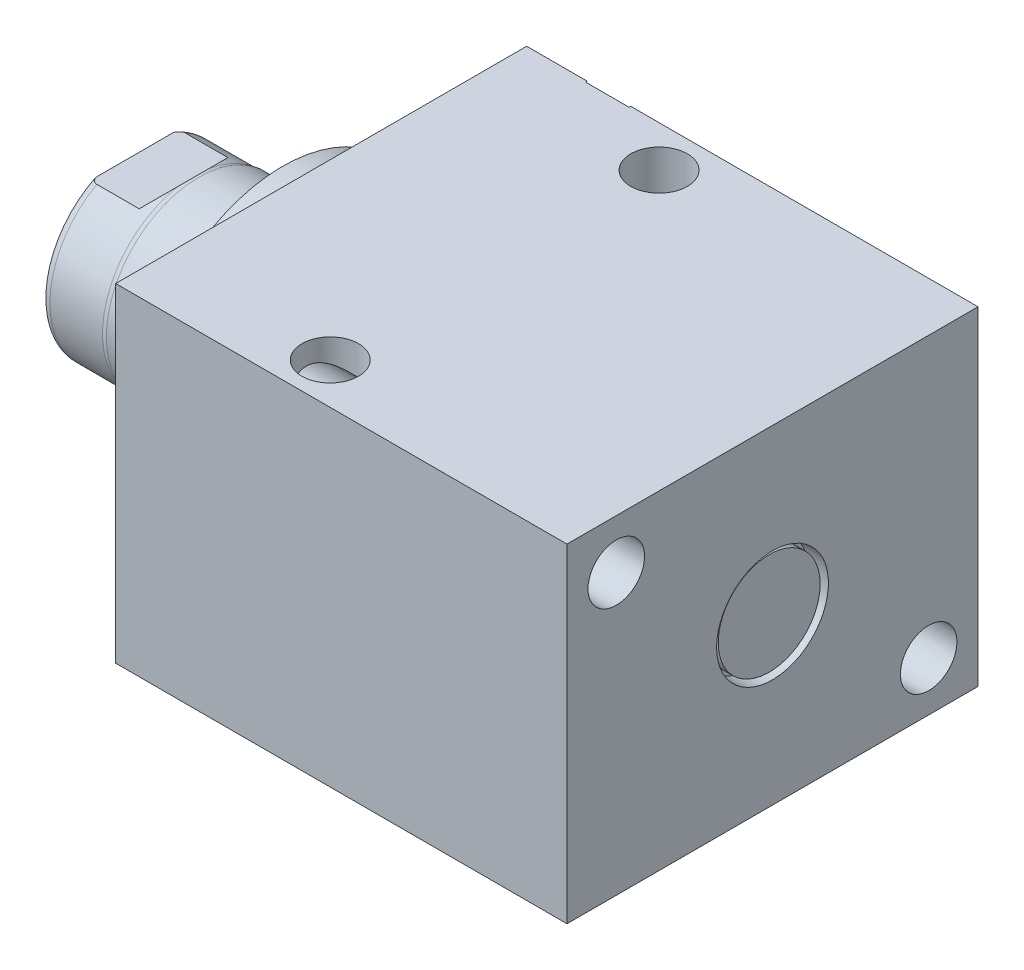
SolidWorks part; units mm, degrees
material "Alloy Steel"
ref_plane "Front Plane" through (0, 0, 0) normal (0, 0, 1) x (1, 0, 0)
ref_plane "Top Plane" through (0, 0, 0) normal (0, 1, 0) x (1, 0, 0)
ref_plane "Right Plane" through (0, 0, 0) normal (1, 0, 0) x (0, 0, -1)
ref_plane "Plane1" through (0, 0, 0) normal (1, 0, 0) x (0, 0, -1)
sketch "Sketch1" plane through (0, 0, 0) normal (1, 0, 0) x (0, 0, -1)
  line L0 (-31.75, 25.4) -> (31.75, 25.4)
  line L1 (31.75, 25.4) -> (31.75, -25.4)
  line L2 (31.75, -25.4) -> (-31.75, -25.4)
  line L3 (-31.75, -25.4) -> (-31.75, 25.4)
  line L4 (0, -24.4475) -> (0, 24.4475) construction
  dimension "D1" = 50.8
  dimension "D2" = 25.4
  dimension "D3" = 63.5
  dimension "D4" = 31.75
extrude "Extrude1" add sketch "Sketch1" along normal blind 69.723
ref_plane "Plane12" through (0, 17.4498, 0) normal (0, 1, 0) x (-1, 0, 0)
sketch "S2D0002" plane through (0, 17.4498, 0) normal (0, 1, 0) x (-1, 0, 0)
  line L0 (-17.7165, -31.496) -> (-21.336, -31.496)
  line L1 (-17.7165, -31.4706) -> (-17.7165, -31.496)
  line L2 (-17.7165, -31.4706) -> (-17.1196, -30.8737)
  line L3 (-17.1196, -30.8737) -> (-17.1196, -18.034)
  line L4 (-17.1196, -18.034) -> (-12.7, -18.034)
  line L5 (-12.7, -18.034) -> (-12.7, -31.75)
  line L6 (-12.7, -19.1384) -> (-12.7, 0.6985) construction
  line L7 (0, -31.75) -> (0, 31.75) construction
  line L8 (-21.336, -31.75) -> (-21.336, -31.496)
  line L9 (-69.723, -31.75) -> (0, -31.75) construction
  line L10 (-21.336, -31.75) -> (-12.7, -31.75)
  dimension "D1" = 13.716
  dimension "D2" = 12.7
  dimension "D3" = 8.8392
  dimension "D4" = 45
  dimension "D5" = 0.6223
  dimension "D6" = 10.033
  dimension "D7" = 0.0254
  dimension "D8" = 0.254
  dimension "D9" = 17.272
revolve "Cut-Revolve1" cut sketch "S2D0002" angle 360 about L6
pattern_linear "LPattern1" count 2 spacing 41.148 along (1, 0, 0) count 2 spacing 17.4498 along (0, -1, 0) skipping (0, 1), (1, 0) of "Cut-Revolve1"
sketch "Sketch5" plane through (0, 0, 0) normal (-1, 0, 0) x (0, 0, 1)
  circle A0 centre (0, 0) radius 22.225
  dimension "D1" = 44.45
extrude "Extrude2" add sketch "Sketch5" along normal blind 5.969
ref_plane "Plane5" through (0, 0, 0) normal (0, -1, 0) x (0, 0, 1)
sketch "Sketch6" plane through (0, 0, 0) normal (0, -1, 0) x (0, 0, 1)
  line L0 (0, 5.969) -> (-14.2748, 5.969)
  line L1 (-14.2748, 5.969) -> (-14.2748, 28.829)
  line L2 (-14.2748, 28.829) -> (0, 28.829)
  line L3 (0, 28.829) -> (0, 5.969)
  line L4 (0, -5.7546) -> (0, 21.1709) construction
  line L5 (22.225, 5.969) -> (-22.225, 5.969) construction
  line L6 (31.75, -69.723) -> (-31.75, -69.723) construction
  dimension "D1" = 98.552
  dimension "D2" = 28.5496
revolve "Revolve1" add sketch "Sketch6" angle 360 about L4
ref_plane "Plane6" through (-18.5113, 3.2639, 0) normal (0, 0, 1) x (0, 1, 0)
sketch "S2D0001" plane through (-18.5113, 3.2639, 0) normal (0, 0, 1) x (0, 1, 0)
  line L0 (1.8669, 8.206) -> (1.8669, -6.5225)
  line L1 (-3.2639, -6.5225) -> (1.8669, -6.5225)
  line L2 (3.0861, 10.3177) -> (-3.2639, 10.3177)
  line L3 (-3.2639, 10.3177) -> (-3.2639, -6.5225)
  line L4 (1.8669, 8.206) -> (3.0861, 10.3177)
  line L5 (-3.2639, -18.5113) -> (-3.2639, 2.765) construction
  line L6 (11.0109, 10.3177) -> (-17.5387, 10.3177) construction
  dimension "D1" = 30
  dimension "D2" = 12.7
  dimension "D3" = 10.2616
  dimension "D4" = 16.8402
  dimension "D5" = 90
revolve "Cut-Revolve4" cut sketch "S2D0001" angle 360 about L5
ref_plane "Plane7" through (0, 0, 0) normal (0, 1, 0) x (0, 0, -1)
sketch "Sketch8" plane through (0, 0, 0) normal (0, 1, 0) x (0, 0, -1)
  line L0 (-14.2748, 18.923) -> (-14.097, 19.685)
  line L1 (-14.097, 19.685) -> (-14.097, 27.813)
  line L2 (0, 12.6594) -> (0, 20.8178) construction
  line L3 (-14.2748, 18.923) -> (-14.2748, 28.829)
  line L4 (-13.7089, 28.829) -> (-14.2748, 28.829)
  line L5 (14.2748, 28.829) -> (-14.2748, 28.829) construction
  line L6 (-14.2748, 28.829) -> (-14.2748, 5.969) construction
  arc A0 (-13.7089, 28.829) -> (-14.097, 27.813) centre (-12.573, 27.813) ccw
  dimension "D2" = 1.524
  dimension "D1" = 28.194
  dimension "D3" = 1.016
  dimension "D4" = 0.762
  dimension "D5" = 9.144
revolve "Cut-Revolve5" cut sketch "Sketch8" angle 360 about L2
ref_plane "Plane11" through (0, 0, 0) normal (0, 0, -1) x (0, -1, 0)
sketch "Sketch12" plane through (0, 0, 0) normal (0, 0, -1) x (0, -1, 0)
  line L0 (12.319, 28.829) -> (12.319, 21.2598)
  line L1 (12.319, 21.2598) -> (14.2748, 19.304)
  line L2 (-12.319, 28.829) -> (-12.319, 21.2598)
  line L3 (-12.319, 21.2598) -> (-14.2748, 19.304)
  line L4 (12.319, 28.829) -> (14.2748, 28.829)
  line L5 (0, 13.7262) -> (0, 20.767) construction
  line L6 (-14.2748, 19.304) -> (-14.2748, 28.829)
  line L7 (14.2748, 5.969) -> (14.2748, 18.923) construction
  line L9 (14.2748, 19.304) -> (14.2748, 28.829)
  line L10 (-12.319, 28.829) -> (-14.2748, 28.829)
  line L12 (13.7089, 28.829) -> (-13.7089, 28.829) construction
  dimension "D1" = 24.638
  dimension "D2" = 7.5692
  dimension "D3" = 45
extrude "Cut-Extrude4" cut sketch "Sketch12" against normal mid plane 60.96
hole_wizard "Hole1" positions "Sketch15" profile "Sketch14" legacy end condition up to next
sketch "Sketch15" plane through (0, 0, 0) normal (-1, 0, 0) x (0, 0, 1)
  line L0 (0, 0) -> (-29.9914, 0) construction
  line L1 (0, 0) -> (0, 25.7648) construction
  point P0 (-24.13, -17.78)
  point P11 (24.13, 17.78)
  dimension "D1" = 17.78
  dimension "D2" = 24.13
  dimension "D3" = 35.56
  dimension "D4" = 48.26
sketch "Sketch14" plane through (0, -17.78, -24.13) normal (0, 1, 0) x (0, 0, 1)
  line L0 (0, 0) -> (0, 69.723)
  line L1 (0, 69.723) -> (4.369, 69.723)
  line L2 (4.369, 69.723) -> (4.369, 0)
  line L3 (4.369, 0) -> (0, 0)
  line L4 (0, 110) -> (0, -10) construction
  dimension "Diameter" = 8.738
  dimension "Depth" = 69.723
hole_wizard "Hole2" positions "Sketch17" profile "Sketch16" legacy
sketch "Sketch17" plane through (0, 25.4, 0) normal (0, 1, 0) x (-1, 0, 0)
  line L0 (0, 0) -> (-59.3363, 0) construction
  line L1 (0, -31.75) -> (0, 31.75) construction
  point P0 (-26.797, -25.4)
  point P9 (-26.797, 25.4)
  dimension "D1" = 50.8
  dimension "D2" = 26.797
  dimension "D3" = 25.4
sketch "Sketch16" plane through (26.797, 25.4, -25.4) normal (1, 0, 0) x (0, 0, 1)
  line L0 (0, 0) -> (0, 50.8)
  line L1 (0, 50.8) -> (4.369, 50.8)
  line L2 (4.369, 50.8) -> (4.369, 0)
  line L3 (4.369, 0) -> (0, 0)
  line L4 (0, 110) -> (0, -10) construction
  dimension "Diameter" = 8.738
  dimension "Depth" = 50.8
sketch "Sketch18" plane through (0, 0, -31.496) normal (0, 0, -1) x (-1, 0, 0)
  line L1 (-46.863, 4.0328) -> (-53.848, 8.0656)
  line L2 (-53.848, 8.0656) -> (-60.833, 4.0328)
  line L3 (-60.833, 4.0328) -> (-60.833, -4.0328)
  line L4 (-60.833, -4.0328) -> (-53.848, -8.0656)
  line L5 (-53.848, -8.0656) -> (-46.863, -4.0328)
  line L6 (-46.863, -4.0328) -> (-46.863, 4.0328)
  circle A0 centre (-53.848, 0) radius 6.985 construction
  circle A1 centre (-53.848, 0) radius 8.636 construction
  dimension "D1" = 13.97
extrude "Extrude3" add sketch "Sketch18" along normal blind 6.78
sketch "Sketch19" plane through (0, 0, 0) normal (0, 1, 0) x (-1, 0, 0)
  line L0 (-53.848, -18.5103) -> (-53.848, -44.3941) construction
  line L2 (-53.848, -38.276) -> (-60.833, -38.276) construction
  line L3 (-60.833, -38.276) -> (-60.833, -31.496) construction
  line L4 (-60.071, -38.276) -> (-60.071, -40.689)
  line L5 (-60.071, -40.689) -> (-63.246, -40.689)
  line L6 (-63.246, -40.689) -> (-63.246, -37.514)
  line L7 (-63.246, -37.514) -> (-60.833, -37.514)
  line L8 (-53.848, -18.034) -> (-53.848, -30.8737) construction
  arc A0 (-60.833, -37.514) -> (-60.071, -38.276) centre (-60.071, -37.514) ccw
  dimension "D1" = 0.762
  dimension "D2" = 3.175
  dimension "D3" = 3.175
revolve "Cut-Revolve6" cut sketch "Sketch19" angle 360 about L0
sketch "Sketch20" plane through (0, 0, 0) normal (0, 1, 0) x (1, 0, 0)
  line L0 (0, 0) -> (70.5114, 0) construction
  line L1 (69.723, 8.636) -> (66.675, 8.636)
  line L2 (69.723, 31.75) -> (69.723, -31.75) construction
  line L3 (66.675, 8.636) -> (66.675, 5.0165)
  line L4 (66.675, 5.0165) -> (66.6496, 5.0165)
  line L5 (66.6496, 5.0165) -> (66.0527, 4.4196)
  line L6 (66.0527, 4.4196) -> (56.1086, 4.4196)
  line L7 (56.1086, 4.4196) -> (56.1086, 0)
  line L8 (56.1086, 0) -> (69.723, 0)
  line L9 (69.723, 0) -> (69.723, 8.636)
  dimension "D1" = 17.272
  dimension "D2" = 3.048
  dimension "D3" = 10.033
  dimension "D4" = 0.0254
  dimension "D5" = 45
  dimension "D6" = 8.8392
  dimension "D7" = 10.5664
revolve "Cut-Revolve7" cut sketch "Sketch20" angle 360 about L0
sketch "Sketch21" plane through (66.675, 0, 0) normal (1, 0, 0) x (0, 0, -1)
  circle A0 centre (0, 0) radius 7.874
  dimension "D1" = 15.748
extrude "Extrude4" add sketch "Sketch21" along normal blind 2.54
